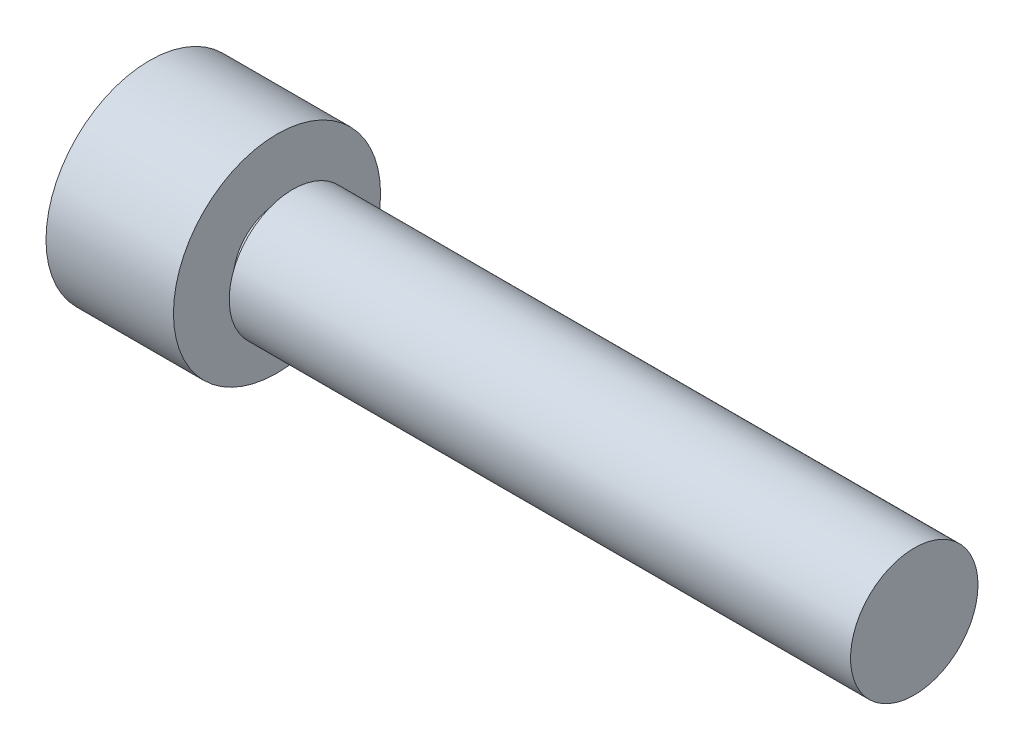
SolidWorks part; units mm, degrees
ref_plane "Front Plane" through (0, 0, 0) normal (0, 0, 1) x (1, 0, 0)
ref_plane "Top Plane" through (0, 0, 0) normal (0, 1, 0) x (1, 0, 0)
ref_plane "Right Plane" through (0, 0, 0) normal (1, 0, 0) x (0, 0, -1)
sketch "Sketch2" plane through (0, 0, 0) normal (0, 1, 0) x (1, 0, 0)
  line L0 (0, 0) -> (-46.6, 0)
  line L1 (0, 0) -> (0, 4)
  line L4 (-48, 6.5) -> (-48, 0)
  line L6 (-46.6, 0) -> (-48, 0)
  line L7 (0, 4) -> (-39, 4)
  line L8 (-39, 4) -> (-39, 2.75)
  line L9 (-39, 2.75) -> (-40, 2.75)
  line L10 (-48, 6.5) -> (-40, 6.5)
  line L11 (-40, 6.5) -> (-40, 2.75)
  point P3 (-41.8447, 2.75)
  dimension "D1" = 4
  dimension "D2" = 8
  dimension "D3" = 48
  dimension "D4" = 6.5
  dimension "D5" = 2.75
  dimension "D6" = 1
revolve "Revolve1" add sketch "Sketch2" angle 360 about L0
